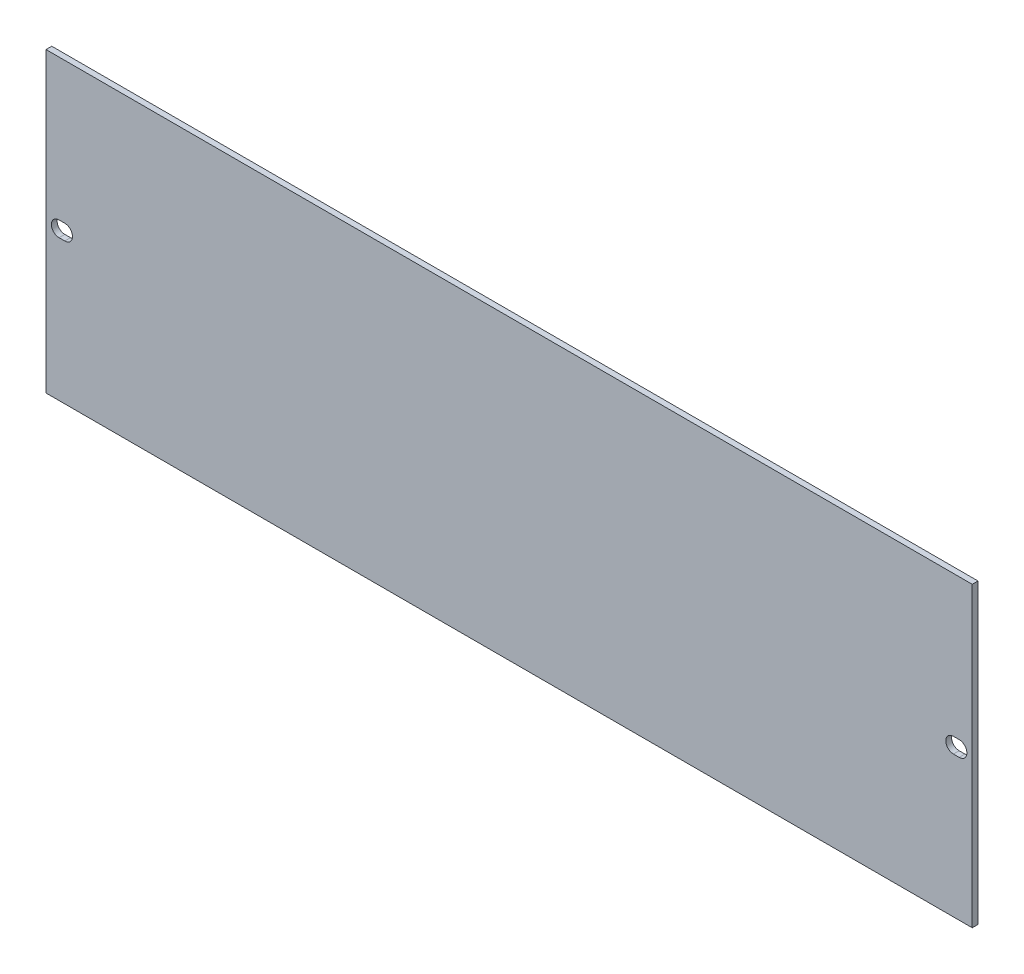
SolidWorks part; units mm, degrees
ref_plane "Alzado" through (0, 0, 0) normal (0, 0, 1) x (1, 0, 0)
ref_plane "Planta" through (0, 0, 0) normal (0, 1, 0) x (1, 0, 0)
ref_plane "Vista lateral" through (0, 0, 0) normal (1, 0, 0) x (0, 0, -1)
sketch "Croquis1" plane through (0, 0, 0) normal (0, 0, 1) x (1, 0, 0)
  line L0 (-234.5, 0) -> (-231.5, 0) construction
  line L1 (-241.3, 77.5) -> (241.3, 77.5)
  line L2 (-241.3, 77.5) -> (-241.3, -77.5)
  line L3 (-241.3, -77.5) -> (241.3, -77.5)
  line L4 (241.3, 77.5) -> (241.3, -77.5)
  line L5 (-241.3, 77.5) -> (241.3, -77.5) construction
  line L6 (-241.3, -77.5) -> (241.3, 77.5) construction
  line L7 (-234.5, 4) -> (-231.5, 4)
  line L8 (-234.5, -4) -> (-231.5, -4)
  line L9 (0, 0) -> (0, 132.2792) construction
  line L10 (234.5, 0) -> (231.5, 0) construction
  line L11 (234.5, 4) -> (231.5, 4)
  line L12 (234.5, -4) -> (231.5, -4)
  arc A0 (-234.5, 4) -> (-234.5, -4) centre (-234.5, 0) ccw
  arc A1 (-231.5, -4) -> (-231.5, 4) centre (-231.5, 0) ccw
  arc A2 (234.5, 4) -> (234.5, -4) centre (234.5, 0) cw
  arc A3 (231.5, -4) -> (231.5, 4) centre (231.5, 0) cw
  point P0 (0, 0)
  point P8 (-233, 0)
  point P17 (233, 0)
  dimension "D1" = 155
  dimension "D2" = 482.6
  dimension "D3" = 233
  dimension "D4" = 8
  dimension "D5" = 3
extrude "Saliente-Extruir1" add sketch "Croquis1" along normal blind 3
